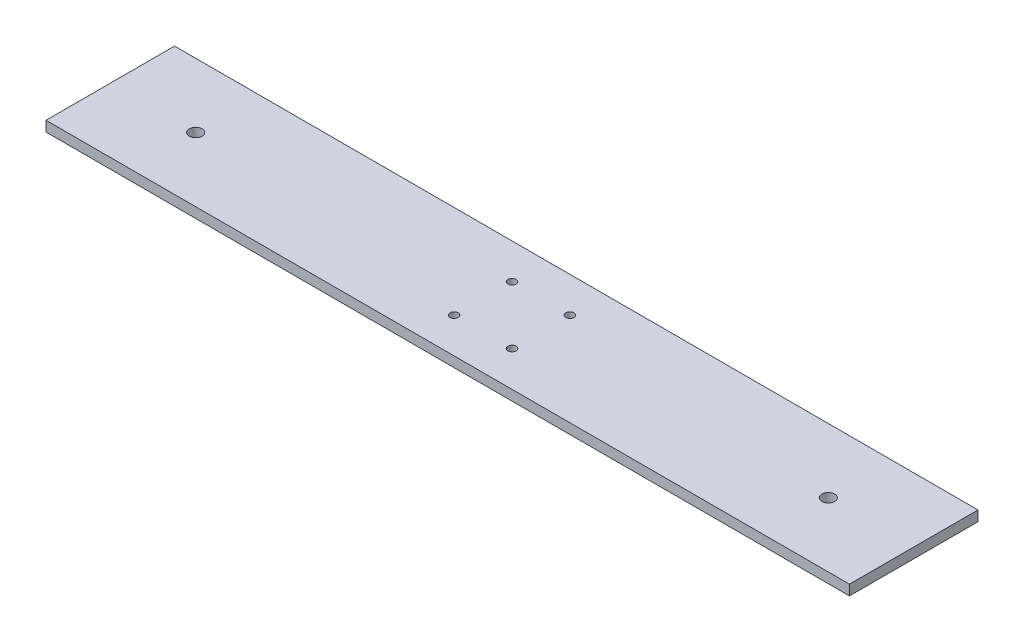
SolidWorks part; units mm, degrees
ref_plane "Front Plane" through (0, 0, 0) normal (0, 0, 1) x (1, 0, 0)
ref_plane "Top Plane" through (0, 0, 0) normal (0, 1, 0) x (1, 0, 0)
ref_plane "Right Plane" through (0, 0, 0) normal (1, 0, 0) x (0, 0, -1)
sketch "Sketch1" plane through (0, 0, 0) normal (0, 1, 0) x (1, 0, 0)
  line L0 (0, 17.6316) -> (0, -17.4211) construction
  line L1 (-25.0526, 0) -> (28.9474, 0) construction
  line L3 (125, -20) -> (-125, -20)
  line L4 (125, -20) -> (125, 20)
  line L5 (125, 20) -> (-125, 20)
  line L6 (-125, -20) -> (-125, 20)
  line L7 (125, -20) -> (-125, 20) construction
  line L8 (125, 20) -> (-125, -20) construction
  circle A0 centre (-98.425, 0) radius 2
  circle A1 centre (98.425, 0) radius 2
  circle A2 centre (-9, 9) radius 1.273
  circle A3 centre (9, 9) radius 1.273
  circle A4 centre (9, -9) radius 1.273
  circle A5 centre (-9, -9) radius 1.273
  point P1 (0, 0)
  dimension "D1" = 40
  dimension "D3" = 4
  dimension "D2" = 250
  dimension "D4" = 196.85
  dimension "D5" = 9
  dimension "D6" = 9
extrude "Boss-Extrude1" add sketch "Sketch1" along normal blind 3.175
equation "\"connector_D1\" = 70 'the big holes diameter"
equation "\"mtg_hole_D\" = 5.5 'mounting holes"
equation "\"mtg_dfc\" = 40 'mounting hole distance from center"
equation "\"plate_thickness\" = 6.35 'thickness of the plate "
equation "\"t_height\" = 200"
equation "\"t_width\" = 240"
equation "\"t_length\" = 240"
equation "\"plate_hole_from_edge\" = 9"
equation "\"plate_spacing\" = 1"
equation "\"front_plate_height\" = \"t_height\" + 38"
equation "\"front_plate_width\" = \"t_width\" + 38"
equation "\"side_plate_height\" = \"front_plate_height\""
equation "\"side_plate_length\" = \"t_length\" + 38"
equation "\"top_plate_width\" = \"front_plate_width\""
equation "\"top_plate_length\" = \"side_plate_length\""
equation "\"itx_support_t_slot_length\" = \"t_width\" + (2 * 20.5)"
equation "\"locomotion_length\" = \"t_length\""
equation "\"locomotion_width\" = \"t_width\""
equation "\"locomotion_height\" = 40"
equation "\"itx_mtg_hole_spacing\" = 40"
equation "\"D1@Boss-Extrude1\"=.125in"
equation "\"emg30_bracket_hole_len\" = 60"
equation "\"emg30_bracket_hole_wid\" = 11"
equation "\"perce_t_height\" = 50"
equation "\"perce_top_width\" = 170"
equation "\"perce_mtg_hole_spacing\" = \"perce_top_width\" - 20"
